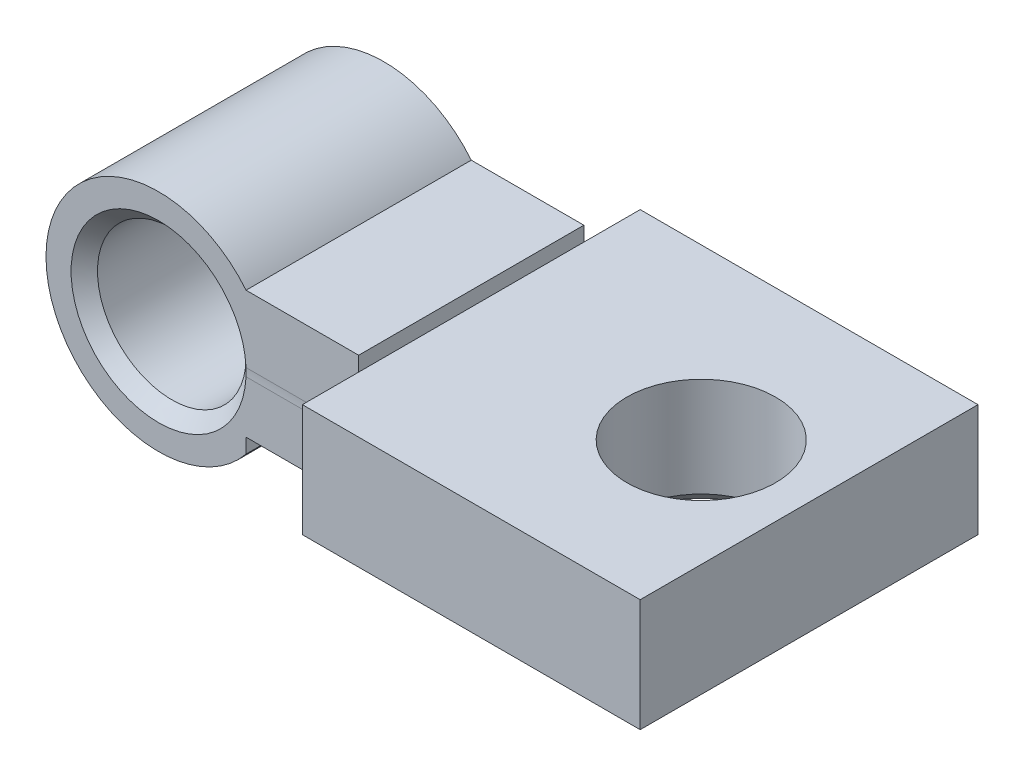
SolidWorks part; units mm, degrees
ref_plane "前视基准面" through (0, 0, 0) normal (0, 0, 1) x (1, 0, 0)
ref_plane "上视基准面" through (0, 0, 0) normal (0, 1, 0) x (1, 0, 0)
ref_plane "右视基准面" through (0, 0, 0) normal (1, 0, 0) x (0, 0, -1)
sketch "草图1" plane through (0, 0, 0) normal (0, 0, 1) x (1, 0, 0)
  circle A0 centre (0, 0) radius 5
extrude "凸台-拉伸1" add sketch "草图1" along normal blind 10
hole_wizard "G1/16 螺纹孔1" positions "草图2" profile "草图3" tap size "G1/16" standard "GB"
sketch "草图2" plane through (0, 0, 10) normal (0, 0, 1) x (1, 0, 0)
  point P0 (0, 0)
sketch "草图3" plane through (0, 0, 10) normal (1, 0, 0) x (0, -1, 0)
  line L0 (0, 0) -> (0, 51.9828)
  line L1 (0, 51.9828) -> (3.3, 50)
  line L2 (3.3, 50) -> (3.3, 0.5865)
  line L3 (3.3, 0.5865) -> (3.8865, 0)
  line L5 (3.8865, 0) -> (0, 0)
  line L6 (-3.3, 0.5865) -> (-3.8865, 0) construction
  line L10 (0, 51.9828) -> (-3.3, 50) construction
  line L11 (0, -6.35) -> (0, 107.95) construction
  dimension "螺纹孔钻头直径" = 6.6
  dimension "螺纹孔钻头深度" = 50
  dimension "近端锥形沉头孔直径" = 7.773
  dimension "近端锥形沉头孔角度" = 90
  dimension "导头角度" = 118
cosmetic thread "孔螺蚊线1" parameters "D1"=15.45, "D2"=7.723
sketch "草图4" plane through (0, 0, 10) normal (0, 0, 1) x (1, 0, 0)
  line L1 (5.675, -6.0927) -> (3.8825, -6.0927)
  line L2 (5.675, -6.0927) -> (5.675, 3.1506)
  line L3 (5.675, 3.1506) -> (3.8825, 3.1506)
  line L4 (3.8825, -6.0927) -> (3.8825, 3.1506)
  line L5 (5.675, -6.0927) -> (3.8825, 3.1506) construction
  line L6 (5.675, 3.1506) -> (3.8825, -6.0927) construction
  circle A0 centre (0, 0) radius 5 construction
  point P0 (4.7787, -1.471)
extrude "切除-拉伸1" cut sketch "草图4" against normal blind 10
sketch "草图5" plane through (3.8825, 0, 0) normal (1, 0, 0) x (0, 0, -1)
  line L2 (0, 3.1506) -> (0, -3.1506) construction
  line L4 (-10, -2.5) -> (0, -2.5)
  line L5 (-10, -2.5) -> (-10, 2.5)
  line L6 (-10, 2.5) -> (0, 2.5)
  line L7 (0, -2.5) -> (0, 2.5)
  line L8 (-10, -2.5) -> (0, 2.5) construction
  line L9 (-10, 2.5) -> (0, -2.5) construction
  point P6 (-5, 0)
extrude "凸台-拉伸2" add sketch "草图5" along normal blind 5
sketch "草图6" plane through (8.8825, 0, 0) normal (1, 0, 0) x (0, 0, -1)
  line L1 (-12.5, -2.5) -> (2.5, -2.5)
  line L2 (-12.5, -2.5) -> (-12.5, 2.5)
  line L3 (-12.5, 2.5) -> (2.5, 2.5)
  line L4 (2.5, -2.5) -> (2.5, 2.5)
  line L5 (-12.5, -2.5) -> (2.5, 2.5) construction
  line L6 (-12.5, 2.5) -> (2.5, -2.5) construction
  point P0 (-5, 0)
extrude "凸台-拉伸3" add sketch "草图6" along normal blind 15
sketch "草图7" plane through (0, -2.5, 0) normal (0, -1, 0) x (-1, 0, 0)
  line L0 (-23.8825, -5) -> (-19.0931, -5)
  line L1 (-23.8825, -12.5) -> (-23.8825, 2.5) construction
hole_wizard "G1/16 螺纹孔2" positions "草图8" profile "草图9" tap size "G1/16" standard "GB"
sketch "草图8" plane through (0, -2.5, 0) normal (0, -1, 0) x (-1, 0, 0)
  point P0 (-19.0931, -5)
sketch "草图9" plane through (19.0931, -2.5, 5) normal (1, 0, 0) x (0, 0, -1)
  line L0 (0, 0) -> (0, 51.9828)
  line L1 (0, 51.9828) -> (3.3, 50)
  line L2 (3.3, 50) -> (3.3, 0.5865)
  line L3 (3.3, 0.5865) -> (3.8865, 0)
  line L5 (3.8865, 0) -> (0, 0)
  line L6 (-3.3, 0.5865) -> (-3.8865, 0) construction
  line L10 (0, 51.9828) -> (-3.3, 50) construction
  line L11 (0, -6.35) -> (0, 107.95) construction
  dimension "螺纹孔钻头直径" = 6.6
  dimension "螺纹孔钻头深度" = 50
  dimension "近端锥形沉头孔直径" = 7.773
  dimension "近端锥形沉头孔角度" = 90
  dimension "导头角度" = 118
cosmetic thread "孔螺蚊线2" parameters "D1"=15.45, "D2"=7.723
